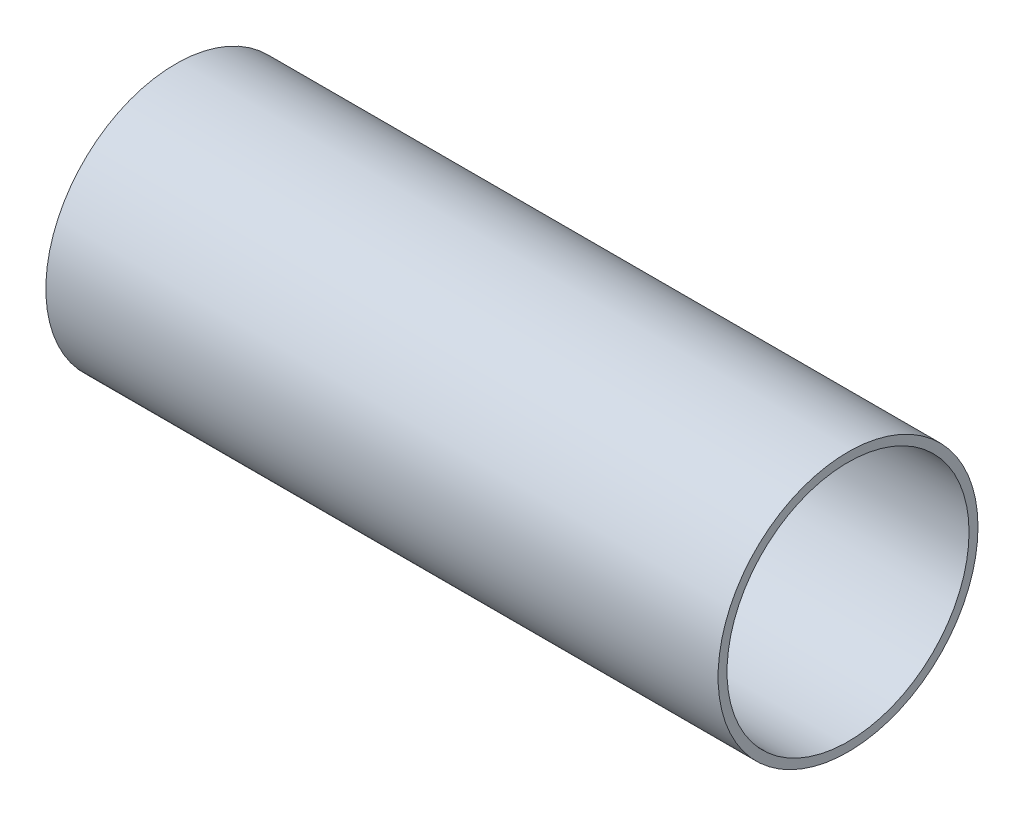
SolidWorks part; units mm, degrees
ref_plane "Front Plane" through (0, 0, 0) normal (0, 0, 1) x (1, 0, 0)
ref_plane "Top Plane" through (0, 0, 0) normal (0, 1, 0) x (1, 0, 0)
ref_plane "Right Plane" through (0, 0, 0) normal (1, 0, 0) x (0, 0, -1)
sketch "Sketch1" plane through (0, 0, 0) normal (1, 0, 0) x (0, 0, -1)
  circle A0 centre (0, 0) radius 29
  circle A1 centre (0, 0) radius 27
  dimension "D1" = 54
  dimension "D2" = 58
extrude "Boss-Extrude1" add sketch "Sketch1" along normal blind 150
